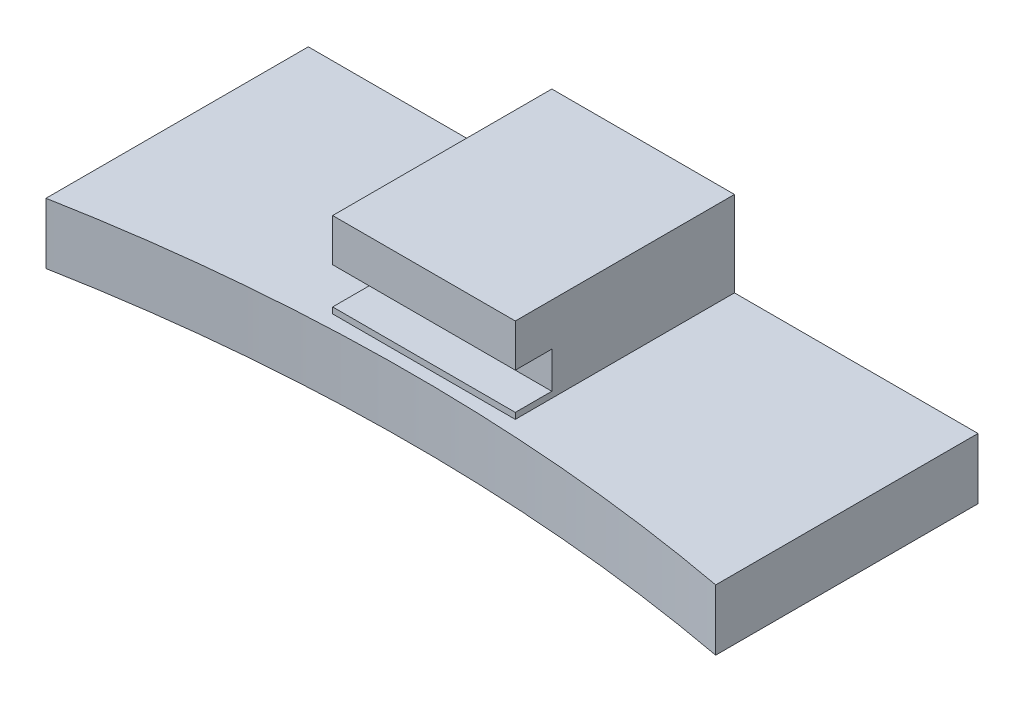
SolidWorks part; units mm, degrees
ref_plane "Front Plane" through (0, 0, 0) normal (0, 0, 1) x (1, 0, 0)
ref_plane "Top Plane" through (0, 0, 0) normal (0, 1, 0) x (1, 0, 0)
ref_plane "Right Plane" through (0, 0, 0) normal (1, 0, 0) x (0, 0, -1)
sketch "Sketch1" plane through (0, 0, 0) normal (0, 1, 0) x (1, 0, 0)
  line L2 (0, 9.9976) -> (0, 31.54)
  line L3 (0, 31.54) -> (55, 31.54)
  line L4 (55, 9.9976) -> (55, 31.54)
  arc A0 (55, 9.9976) -> (0, 9.9976) centre (27.5, -137.46) ccw
  dimension "D4" = 300
  dimension "D3" = 169
  dimension "D1" = 55
  dimension "D2" = 21.5424
extrude "Boss-Extrude1" add sketch "Sketch1" along normal blind 5
sketch "Sketch4" plane through (0, 5, 0) normal (0, 1, 0) x (1, 0, 0)
  line L0 (55, 31.54) -> (0, 31.54) construction
  line L1 (20, 31.54) -> (35, 31.54)
  line L2 (20, 31.54) -> (20, 13.54)
  line L3 (20, 13.54) -> (35, 13.54)
  line L4 (35, 31.54) -> (35, 13.54)
  line L5 (0, 31.54) -> (0, 9.9976) construction
  dimension "D1" = 15
  dimension "D2" = 18
  dimension "D3" = 20
extrude "Boss-Extrude2" add sketch "Sketch4" along normal blind 0.5
sketch "Sketch5" plane through (0, 5.5, 0) normal (0, 1, 0) x (1, 0, 0)
  line L0 (35, 13.54) -> (35, 31.54) construction
  line L1 (20, 31.54) -> (35, 31.54)
  line L2 (20, 31.54) -> (20, 16.54)
  line L3 (20, 16.54) -> (35, 16.54)
  line L4 (35, 31.54) -> (35, 16.54)
  dimension "D1" = 15
extrude "Boss-Extrude3" add sketch "Sketch5" along normal blind 3
sketch "Sketch6" plane through (0, 8.5, 0) normal (0, 1, 0) x (1, 0, 0)
  line L0 (35, 16.54) -> (35, 31.54) construction
  line L1 (20, 31.54) -> (35, 31.54)
  line L2 (20, 31.54) -> (20, 13.54)
  line L3 (20, 13.54) -> (35, 13.54)
  line L4 (35, 31.54) -> (35, 13.54)
  dimension "D1" = 18
extrude "Boss-Extrude4" add sketch "Sketch6" along normal blind 3.5
sketch "Sketch9" plane through (0, 0, -31.54) normal (0, 0, -1) x (-1, 0, 0)
  line L0 (0, 5) -> (0, 0) construction
  line L1 (-55, 0) -> (0, 0) construction
  circle A0 centre (-27.5, 6.5) radius 4.5
  dimension "D1" = 27.5
  dimension "D3" = 9
  dimension "D2" = 6.5
extrude "Cut-Extrude1" cut sketch "Sketch9" against normal blind 4
hole_wizard "M8x1.0 Tapped Hole1" positions "Sketch11" profile "Sketch10" tap size "M8x1.0" standard "ANSI Metric"
sketch "Sketch11" plane through (0, 0, -27.54) normal (0, 0, -1) x (-1, 0, 0)
  point P0 (-27.5, 6.5)
sketch "Sketch10" plane through (27.5, 6.5, -27.54) normal (1, 0, 0) x (0, 1, 0)
  line L0 (0, 0) -> (0, 10.103)
  line L1 (0, 10.103) -> (3.5, 8)
  line L2 (3.5, 8) -> (3.5, 0.525)
  line L3 (3.5, 0.525) -> (4.025, 0)
  line L5 (4.025, 0) -> (0, 0)
  line L6 (-3.5, 0.525) -> (-4.025, 0) construction
  line L10 (0, 10.103) -> (-3.5, 8) construction
  line L11 (0, -6.35) -> (0, 107.95) construction
  dimension "Tap Drill Dia." = 7
  dimension "Tap Drill Depth" = 8
  dimension "Near C'Sink Dia." = 8.05
  dimension "Near C'Sink Angle" = 90
  dimension "Drill Angle" = 118
cosmetic thread "Hole Thread1" parameters "D1"=8, "D2"=8
